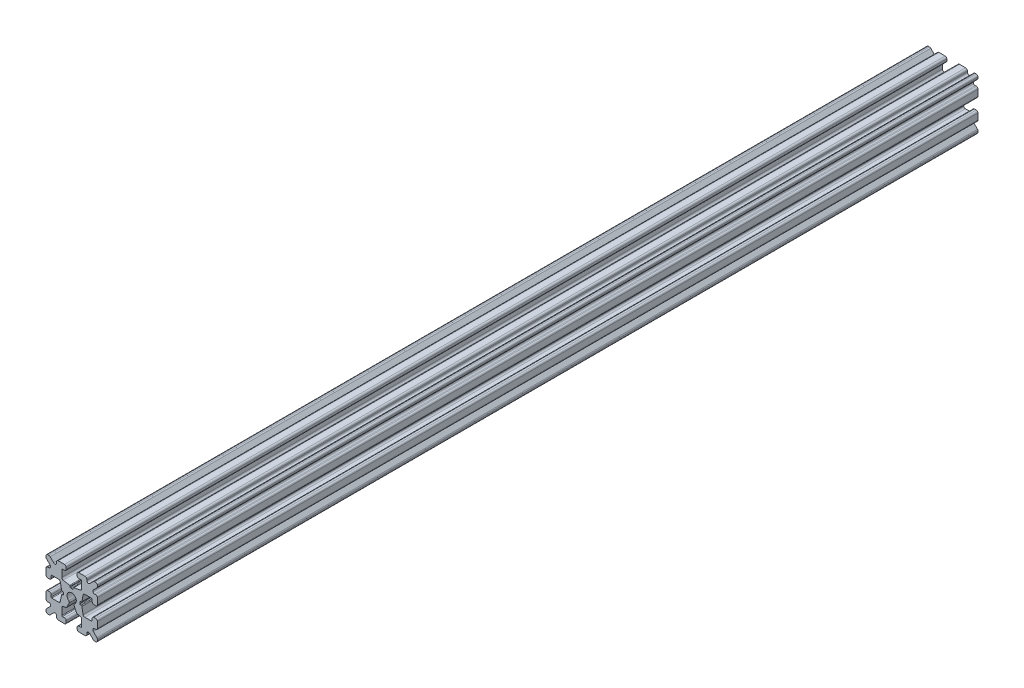
SolidWorks part; units mm, degrees
ref_plane "Front Plane" through (0, 0, 0) normal (0, 0, 1) x (1, 0, 0)
ref_plane "Top Plane" through (0, 0, 0) normal (0, 1, 0) x (1, 0, 0)
ref_plane "Right Plane" through (0, 0, 0) normal (1, 0, 0) x (0, 0, -1)
sketch "Sketch1" plane through (0, 0, 0) normal (0, 0, 1) x (1, 0, 0)
  line L1 (-7.5, -7.5) -> (7.5, -7.5)
  line L2 (-7.5, -7.5) -> (-7.5, 7.5)
  line L3 (-7.5, 7.5) -> (7.5, 7.5)
  line L4 (7.5, -7.5) -> (7.5, 7.5)
  line L5 (-7.5, -7.5) -> (7.5, 7.5) construction
  line L6 (-7.5, 7.5) -> (7.5, -7.5) construction
  circle A0 centre (0, 0) radius 1.35
  point P0 (0, 0)
  dimension "D2" = 2.7
  dimension "D1" = 15
extrude "Boss-Extrude1" add sketch "Sketch1" along normal mid plane 257.1
fillet "Fillet1" radius 0.5 4 edges at (7.5, -7.5, 0) (-7.5, -7.5, 0) (7.5, 7.5, 0) (-7.5, 7.5, 0)
sketch "Sketch2" plane through (0, 0, 128.55) normal (0, 0, 1) x (1, 0, 0)
  line L0 (-7.5, 7) -> (-7.5, -7) construction
  line L1 (-7.5, 1.6) -> (-6, 1.6)
  line L2 (-7.5, 1.6) -> (-7.5, -1.6)
  line L3 (-7.5, -1.6) -> (-6, -1.6)
  line L4 (-6, 1.6) -> (-6, 2.9)
  line L5 (0, 0) -> (-12.1036, 0) construction
  line L6 (-6, -2.9) -> (-3.4, -2.9)
  line L7 (0, 0) -> (-7, 7) construction
  line L8 (-6, 2.9) -> (-3.4, 2.9)
  line L9 (-3.4, -2.9) -> (-3.4, 2.9)
  line L10 (55, 0) -> (-55, 0) construction
  line L11 (-6, -2.9) -> (-6, -1.6)
  line L12 (2.9, 6) -> (1.6, 6)
  line L13 (2.9, 3.4) -> (-2.9, 3.4)
  line L14 (-2.9, 6) -> (-2.9, 3.4)
  line L15 (2.9, 6) -> (2.9, 3.4)
  line L16 (-1.6, 6) -> (-2.9, 6)
  line L17 (1.6, 7.5) -> (1.6, 6)
  line L18 (-1.6, 7.5) -> (1.6, 7.5)
  line L19 (-1.6, 7.5) -> (-1.6, 6)
  line L20 (-1.6, -7.5) -> (-1.6, -6)
  line L21 (-1.6, -7.5) -> (1.6, -7.5)
  line L22 (1.6, -7.5) -> (1.6, -6)
  line L23 (-1.6, -6) -> (-2.9, -6)
  line L24 (2.9, -6) -> (2.9, -3.4)
  line L25 (-2.9, -6) -> (-2.9, -3.4)
  line L26 (2.9, -3.4) -> (-2.9, -3.4)
  line L27 (2.9, -6) -> (1.6, -6)
  line L28 (6, -2.9) -> (6, -1.6)
  line L29 (3.4, -2.9) -> (3.4, 2.9)
  line L30 (6, 2.9) -> (3.4, 2.9)
  line L31 (6, -2.9) -> (3.4, -2.9)
  line L32 (6, 1.6) -> (6, 2.9)
  line L33 (7.5, -1.6) -> (6, -1.6)
  line L34 (7.5, 1.6) -> (7.5, -1.6)
  line L35 (7.5, 1.6) -> (6, 1.6)
  dimension "D1" = 3.2
  dimension "D2" = 5.8
  dimension "D3" = 1.5
  dimension "D4" = 2.6
extrude "Cut-Extrude1" cut sketch "Sketch2" against normal through all
sketch "Sketch4" plane through (0, 0, 128.55) normal (0, 0, 1) x (1, 0, 0)
  line L0 (-3.4, 2.9) -> (-2.85, 0)
  line L1 (55, 0) -> (-55, 0) construction
  line L2 (-2.85, 0) -> (-3.4, -2.9)
  line L3 (-3.4, -2.9) -> (-3.4, 2.9) construction
  line L4 (-3.4, 2.9) -> (-3.4, -2.9)
  line L5 (-2.9, 3.4) -> (0, 2.85)
  line L6 (0, 2.85) -> (2.9, 3.4)
  line L7 (2.9, 3.4) -> (-2.9, 3.4)
  line L8 (3.4, 2.9) -> (2.85, 0)
  line L9 (2.85, 0) -> (3.4, -2.9)
  line L10 (3.4, -2.9) -> (3.4, 2.9)
  line L11 (-2.9, -3.4) -> (0, -2.85)
  line L12 (0, -2.85) -> (2.9, -3.4)
  line L13 (2.9, -3.4) -> (-2.9, -3.4)
  circle A2 centre (0, 0) radius 2.85
  circle A3 centre (0, 0) radius 2.85 construction
  dimension "D1" = 1.5
extrude "Cut-Extrude3" cut sketch "Sketch4" against normal through all
fillet "Fillet3" radius 0.5 16 edges at (-6, -1.6, 0) (-7.5, -1.6, 0) (-6, 1.6, 0) (-7.5, 1.6, 0) (-1.6, -7.5, 0) (-1.6, -6, 0) (1.6, -7.5, 0) (1.6, -6, 0) (6, -1.6, 0) (7.5, -1.6, 0) (7.5, 1.6, 0) (6, 1.6, 0) (1.6, 7.5, 0) (1.6, 6, 0) (-1.6, 7.5, 0) (-1.6, 6, 0)
fillet "Fillet4" radius 0.5 8 edges at (-3.4, 2.9, 0) (-3.4, -2.9, 0) (2.9, -3.4, 0) (-2.9, -3.4, 0) (3.4, -2.9, 0) (3.4, 2.9, 0) (-2.9, 3.4, 0) (2.9, 3.4, 0)
fillet "Fillet5" radius 3 4 edges at (0, -2.85, 0) (2.85, 0, 0) (-2.85, 0, 0) (0, 2.85, 0)
fillet "Fillet6" radius 0.2 8 edges at (-2.9, -6, 0) (2.9, -6, 0) (6, -2.9, 0) (6, 2.9, 0) (2.9, 6, 0) (-2.9, 6, 0) (-6, -2.9, 0) (-6, 2.9, 0)
sketch "Sketch5" plane through (0, 0, 128.55) normal (0, 0, 1) x (1, 0, 0)
  line L0 (0, 0) -> (-7, 7) construction
  line L1 (-7.5, 6.4393) -> (-5.4607, 4.4)
  line L2 (-6.4393, 7.5) -> (-4.4, 5.4607)
  line L3 (-7.5, 4.4) -> (-5.4607, 4.4)
  line L4 (-3.8141, 2.9) -> (-5.8, 2.9) construction
  line L5 (0, 0) -> (-12.1819, 0) construction
  line L6 (-4.4, 7.5) -> (-4.4, 5.4607)
  line L7 (-2.9, 5.8) -> (-2.9, 3.8141) construction
  line L8 (-7.5, 6.4393) -> (-7.5, 4.4)
  line L9 (-7.5, 7) -> (-7.5, 2.1) construction
  line L10 (2.1, -7.5) -> (7, -7.5) construction
  line L11 (7.5, -7) -> (7.5, -2.1) construction
  line L12 (7, 7.5) -> (2.1, 7.5) construction
  line L13 (-2.1, 7.5) -> (-7, 7.5) construction
  line L14 (-4.4, 7.5) -> (-6.4393, 7.5)
  line L16 (55, 0) -> (-55, 0) construction
  line L17 (0, 0) -> (0, 10.993) construction
  line L18 (0, -54.6431) -> (0, 54.6431) construction
  line L20 (4.4, 7.5) -> (6.4393, 7.5)
  line L22 (7.5, 6.4393) -> (7.5, 4.4)
  line L23 (4.4, 7.5) -> (4.4, 5.4607)
  line L24 (7.5, 4.4) -> (5.4607, 4.4)
  line L25 (6.4393, 7.5) -> (4.4, 5.4607)
  line L26 (7.5, 6.4393) -> (5.4607, 4.4)
  line L27 (7.5, -6.4393) -> (5.4607, -4.4)
  line L28 (6.4393, -7.5) -> (4.4, -5.4607)
  line L29 (7.5, -4.4) -> (5.4607, -4.4)
  line L30 (4.4, -7.5) -> (4.4, -5.4607)
  line L31 (7.5, -6.4393) -> (7.5, -4.4)
  line L33 (4.4, -7.5) -> (6.4393, -7.5)
  line L36 (-4.4, -7.5) -> (-6.4393, -7.5)
  line L38 (-7.5, -6.4393) -> (-7.5, -4.4)
  line L39 (-4.4, -7.5) -> (-4.4, -5.4607)
  line L40 (-7.5, -4.4) -> (-5.4607, -4.4)
  line L41 (-6.4393, -7.5) -> (-4.4, -5.4607)
  line L42 (-7.5, -6.4393) -> (-5.4607, -4.4)
  dimension "D1" = 1.5
  dimension "D2" = 1.5
  dimension "D3" = 1.5
extrude "Cut-Extrude4" cut sketch "Sketch5" against normal through all
fillet "Fillet8" radius 0.5 24 edges at (-5.4607, 4.4, 0) (-7.5, 4.4, 0) (-5.4607, -4.4, 0) (-7.5, -4.4, 0) (-4.4, -7.5, 0) (-4.4, -5.4607, 0) (4.4, -7.5, 0) (4.4, -5.4607, 0) (5.4607, -4.4, 0) (7.5, -4.4, 0) (7.5, 4.4, 0) (5.4607, 4.4, 0) (4.4, 5.4607, 0) (4.4, 7.5, 0) (-4.4, 5.4607, 0) (-4.4, 7.5, 0) (-6.4393, 7.5, 0) (-7.5, 6.4393, 0) (6.4393, 7.5, 0) (7.5, 6.4393, 0) (6.4393, -7.5, 0) (7.5, -6.4393, 0) (-6.4393, -7.5, 0) (-7.5, -6.4393, 0)
sketch "Sketch6" plane through (0, 0, 128.55) normal (0, 0, 1) x (1, 0, 0)
  line L0 (0, 0) -> (0, 11.013) construction
  line L1 (0.559, 2.956) -> (2.1235, 2.956) construction
  line L2 (0, -54.6431) -> (0, 54.6431) construction
  line L3 (0, 0) -> (7, 7) construction
  line L4 (8.6552, 0.4445) -> (8.6552, -0.4445)
  line L5 (2.406, 0.4445) -> (8.6552, 0.4445)
  line L8 (2.406, -0.4445) -> (2.406, 0.4445)
  line L10 (8.6552, -0.4445) -> (2.406, -0.4445)
  line L11 (-8.6552, -0.4445) -> (-2.406, -0.4445)
  line L12 (-2.406, -0.4445) -> (-2.406, 0.4445)
  line L14 (-0.4445, 8.6552) -> (-0.4445, 2.406)
  line L15 (-0.4445, 2.406) -> (0.4445, 2.406)
  line L17 (0.4445, 2.406) -> (0.4445, 8.6552)
  line L18 (0.4445, 8.6552) -> (-0.4445, 8.6552)
  line L20 (-2.406, 0.4445) -> (-8.6552, 0.4445)
  line L21 (-8.6552, 0.4445) -> (-8.6552, -0.4445)
  point P7 (0, 2.5973)
  dimension "D3" = 0.55
  dimension "D1" = 0.889
extrude "Cut-Extrude5" cut sketch "Sketch6" against normal through all
sketch "Sketch7" plane through (0, 0, 128.55) normal (0, 0, 1) x (1, 0, 0)
  line L0 (0, 0) -> (-2.1533, -4.6178)
  line L1 (-2.1533, -4.6178) -> (2.1533, -4.6178)
  line L2 (2.1533, -4.6178) -> (0, 0)
  line L3 (0, 0) -> (0, -8.6832) construction
  line L4 (0, -54.6431) -> (0, 54.6431) construction
  dimension "D1" = 50
extrude "Cut-Extrude6" cut sketch "Sketch7" against normal through all
fillet "Fillet9" radius 0.5 4 edges at (0.5705, -1.2235, 0) (-0.5705, -1.2235, 0) (1.4579, -3.1265, 0) (-1.4579, -3.1265, 0)
fillet "Fillet10" radius 0.2 12 edges at (-2.406, 0.4445, 0) (-2.406, -0.4445, 0) (0.4445, 2.406, 0) (-0.4445, 2.406, 0) (2.406, 0.4445, 0) (2.406, -0.4445, 0) (-2.9366, -0.4445, 0) (-2.9366, 0.4445, 0) (2.9366, -0.4445, 0) (2.9366, 0.4445, 0) (0.4445, 2.9366, 0) (-0.4445, 2.9366, 0)
sketch "Sketch10" plane through (0, 0, 128.55) normal (0, 0, 1) x (1, 0, 0)
  line L0 (2.7, 6) -> (2.1, 6) construction
  line L1 (-2.75, 6) -> (2.75, 6)
  line L2 (-2.75, 6) -> (-2.75, 3.6)
  line L3 (-2.75, 3.6) -> (2.75, 3.6)
  line L4 (2.75, 6) -> (2.75, 3.6)
  line L5 (0, 0) -> (0, 8.8277) construction
  line L6 (-3.2398, 3.994) -> (-2.2083, 2.8606) construction
  line L7 (-3.878, 3.2131) -> (-3.2018, 2.4701) construction
  line L8 (-2.406, -0.2445) -> (-2.406, 0.2445) construction
  line L9 (-2.1, 7.5) -> (-3.9, 7.5) construction
  line L10 (-1.5, 7.5) -> (1.5, 7.5)
  line L11 (-1.5, 7.5) -> (-1.5, 3.5)
  line L12 (-1.5, 3.5) -> (1.5, 3.5)
  line L13 (1.5, 7.5) -> (1.5, 3.5)
  arc A1 (-3.3228, 2.4932) -> (-3.8141, 2.9) centre (-3.8141, 2.4) ccw construction
  arc A2 (-2.9, 3.8141) -> (-2.4932, 3.3228) centre (-2.4, 3.8141) ccw construction
  arc A3 (0.88, -1.0238) -> (-0.88, -1.0238) centre (0, 0) ccw construction
  point P19 (-1.35, 0)
  point P20 (-2.406, 0)
  dimension "D1" = 2.4
  dimension "D2" = 5.5
  dimension "D3" = 0.9976
  dimension "D4" = 3
  dimension "D5" = 4
sketch "Sketch11" plane through (0, 0, 128.55) normal (0, 0, 1) x (1, 0, 0)
  line L0 (-7.5, 7) -> (-7.5, 6.6464) construction
  line L1 (-7.5, 7.5) -> (7.5, 7.5) construction
  line L2 (-7.5, 7.5) -> (-7.5, -7.5) construction
  line L3 (-7.5, -7.5) -> (7.5, -7.5) construction
  line L4 (7.5, 7.5) -> (7.5, -7.5) construction
  line L5 (-7, -7.5) -> (-6.6464, -7.5) construction
  line L6 (7.5, 6.6464) -> (7.5, 7) construction
  line L7 (-2.1, 7.5) -> (-3.9, 7.5) construction
  point P0 (0, 7.5)
  point P1 (0, -7.5)
  point P2 (7.5, 0)
  point P3 (-7.5, 0)
sketch "Sketch12" plane through (0, 0, -128.55) normal (0, 0, -1) x (-1, 0, 0)
  line L1 (-7.5, -7.5) -> (7.5, -7.5) construction
  line L2 (-7.5, -7.5) -> (-7.5, 7.5) construction
  line L3 (-7.5, 7.5) -> (7.5, 7.5) construction
  line L4 (7.5, -7.5) -> (7.5, 7.5) construction
  point P4 (-7.5, 0)
  point P9 (0, -7.5)
  point P10 (7.5, 0)
  point P11 (0, 7.5)
sketch "Sketch13" plane through (0, -7.5, 0) normal (0, -1, 0) x (1, 0, 0)
  line L0 (0, 128.55) -> (0, -128.55) construction
  line L1 (-7.5, -128.55) -> (-7.5, 128.55) construction
  line L2 (7.5, 128.55) -> (7.5, -128.55) construction
sketch "Sketch14" plane through (-7.5, 0, 0) normal (-1, 0, 0) x (0, 0, 1)
  line L0 (128.55, 0) -> (-128.55, 0) construction
sketch "Sketch15" plane through (0, 7.5, 0) normal (0, 1, 0) x (1, 0, 0)
  line L0 (0, -128.55) -> (0, 128.55) construction
  line L1 (-7.5, -128.55) -> (7.5, -128.55) construction
  line L2 (-7.5, -128.55) -> (-7.5, 128.55) construction
  line L3 (7.5, 128.55) -> (7.5, -128.55) construction
sketch "Sketch16" plane through (7.5, 0, 0) normal (1, 0, 0) x (0, 0, -1)
  line L0 (-128.55, 0) -> (128.55, 0) construction
